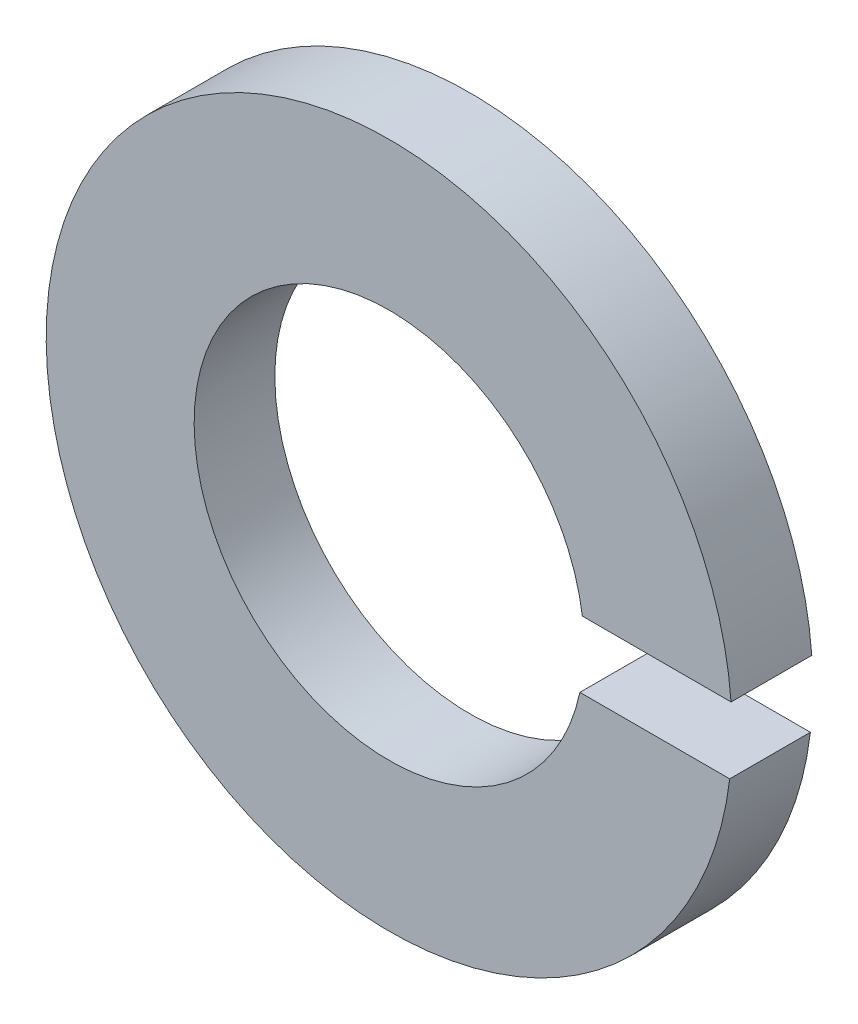
SolidWorks part; units mm, degrees
material "AISI Type A2 Tool Steel"
ref_plane "Front" through (0, 0, 0) normal (0, 0, 1) x (1, 0, 0)
ref_plane "Top" through (0, 0, 0) normal (0, 1, 0) x (1, 0, 0)
ref_plane "Right" through (0, 0, 0) normal (1, 0, 0) x (0, 0, -1)
sketch "Sketch1" plane through (0, 0, 0) normal (0, 0, 1) x (1, 0, 0)
  line L0 (3.3223, -0.3022) -> (0.5645, -0.3022)
  line L1 (3.3223, -0.3022) -> (3.3223, 0.1978)
  line L2 (0.5645, -0.3022) -> (0.5645, 0.1978)
  line L3 (3.3223, 0.1978) -> (0.5645, 0.1978)
  line L4 (3.3223, -0.3022) -> (0.5645, 0.1978) construction
  line L5 (0.5645, -0.3022) -> (3.3223, 0.1978) construction
  arc A0 (1.4364, 0.1978) -> (1.4182, -0.3022) centre (0, 0) ccw
  arc A1 (2.5423, 0.1978) -> (2.532, -0.3022) centre (0, 0) ccw
  point P5 (1.9434, -0.0522)
  dimension "D1" = 2.9
  dimension "D2" = 5.1
  dimension "D3" = 0.5
extrude "Boss-Extrude1" add sketch "Sketch1" along normal blind 0.6 contours L3 A1 L0 A0
